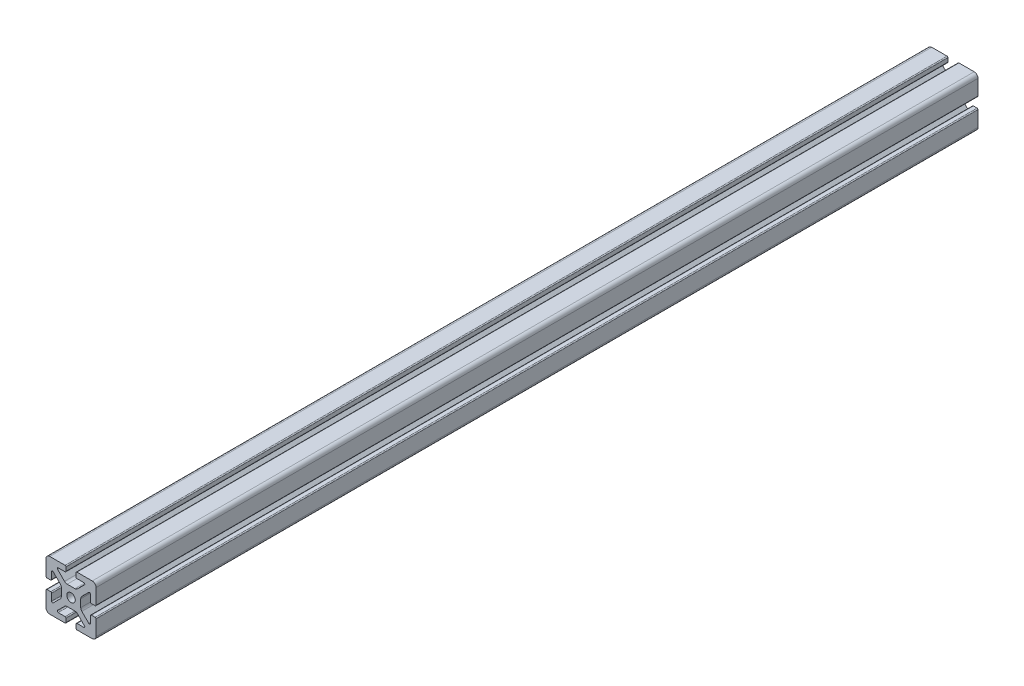
SolidWorks part; units mm, degrees
ref_plane "Front Plane" through (0, 0, 0) normal (0, 0, 1) x (1, 0, 0)
ref_plane "Top Plane" through (0, 0, 0) normal (0, 1, 0) x (1, 0, 0)
ref_plane "Right Plane" through (0, 0, 0) normal (1, 0, 0) x (0, 0, -1)
sketch "Sketch1" plane through (0, 0, 0) normal (0, 0, 1) x (1, 0, 0)
  line L2 (-20, 16.952) -> (-20, 4.7625)
  line L3 (-16.952, 20) -> (-4.7625, 20)
  line L4 (-4.0005, 19.238) -> (-4.0005, 16.2662)
  line L5 (-4.7625, 15.5042) -> (-10.2235, 15.5042)
  line L6 (-10.7623, 14.2034) -> (-5.194, 8.6351)
  line L7 (-14.2034, 10.7623) -> (-8.6351, 5.194)
  line L8 (-15.5042, 10.2235) -> (-15.5042, 4.7625)
  line L9 (-16.2662, 4.0005) -> (-19.238, 4.0005)
  line L11 (-3.0746, 7.7572) -> (3.0746, 7.7572)
  line L12 (-7.7572, 3.0746) -> (-7.7572, -3.0746)
  line L13 (16.2662, 4.0005) -> (19.238, 4.0005)
  line L14 (15.5042, 10.2235) -> (15.5042, 4.7625)
  line L15 (20, 16.952) -> (20, 4.7625)
  line L16 (16.952, 20) -> (4.7625, 20)
  line L17 (4.0005, 19.238) -> (4.0005, 16.2662)
  line L18 (4.7625, 15.5042) -> (10.2235, 15.5042)
  line L19 (7.7572, 3.0746) -> (7.7572, -3.0746)
  line L20 (10.7623, 14.2034) -> (5.194, 8.6351)
  line L21 (14.2034, 10.7623) -> (8.6351, 5.194)
  line L22 (-16.2662, -4.0005) -> (-19.238, -4.0005)
  line L23 (-15.5042, -10.2235) -> (-15.5042, -4.7625)
  line L24 (-14.2034, -10.7623) -> (-8.6351, -5.194)
  line L25 (-10.7623, -14.2034) -> (-5.194, -8.6351)
  line L26 (-4.7625, -15.5042) -> (-10.2235, -15.5042)
  line L27 (-4.0005, -19.238) -> (-4.0005, -16.2662)
  line L28 (-16.952, -20) -> (-4.7625, -20)
  line L29 (-20, -16.952) -> (-20, -4.7625)
  line L30 (20, -16.952) -> (20, -4.7625)
  line L31 (16.952, -20) -> (4.7625, -20)
  line L32 (4.0005, -19.238) -> (4.0005, -16.2662)
  line L33 (4.7625, -15.5042) -> (10.2235, -15.5042)
  line L34 (10.7623, -14.2034) -> (5.194, -8.6351)
  line L35 (14.2034, -10.7623) -> (8.6351, -5.194)
  line L36 (15.5042, -10.2235) -> (15.5042, -4.7625)
  line L37 (16.2662, -4.0005) -> (19.238, -4.0005)
  line L38 (-3.0746, -7.7572) -> (3.0746, -7.7572)
  circle A0 centre (0, 0) radius 3.4036
  arc A1 (-20, 16.952) -> (-16.952, 20) centre (-16.952, 16.952) cw
  arc A2 (-14.2034, 10.7623) -> (-15.5042, 10.2235) centre (-14.7422, 10.2235) ccw
  arc A3 (-10.2235, 15.5042) -> (-10.7623, 14.2034) centre (-10.2235, 14.7422) ccw
  arc A4 (-4.7625, 20) -> (-4.0005, 19.238) centre (-4.7625, 19.238) cw
  arc A5 (-20, 4.7625) -> (-19.238, 4.0005) centre (-19.238, 4.7625) ccw
  arc A6 (-15.5042, 4.7625) -> (-16.2662, 4.0005) centre (-16.2662, 4.7625) cw
  arc A7 (-4.0005, 16.2662) -> (-4.7625, 15.5042) centre (-4.7625, 16.2662) cw
  arc A8 (-3.0746, 7.7572) -> (-5.194, 8.6351) centre (-3.0746, 10.7544) cw
  arc A9 (-7.7572, 3.0746) -> (-8.6351, 5.194) centre (-10.7544, 3.0746) ccw
  arc A10 (15.5042, 4.7625) -> (16.2662, 4.0005) centre (16.2662, 4.7625) ccw
  arc A11 (20, 4.7625) -> (19.238, 4.0005) centre (19.238, 4.7625) cw
  arc A12 (20, 16.952) -> (16.952, 20) centre (16.952, 16.952) ccw
  arc A13 (4.7625, 20) -> (4.0005, 19.238) centre (4.7625, 19.238) ccw
  arc A14 (4.0005, 16.2662) -> (4.7625, 15.5042) centre (4.7625, 16.2662) ccw
  arc A15 (3.0746, 7.7572) -> (5.194, 8.6351) centre (3.0746, 10.7544) ccw
  arc A16 (7.7572, 3.0746) -> (8.6351, 5.194) centre (10.7544, 3.0746) cw
  arc A17 (14.2034, 10.7623) -> (15.5042, 10.2235) centre (14.7422, 10.2235) cw
  arc A18 (10.2235, 15.5042) -> (10.7623, 14.2034) centre (10.2235, 14.7422) cw
  arc A19 (-7.7572, -3.0746) -> (-8.6351, -5.194) centre (-10.7544, -3.0746) cw
  arc A20 (-3.0746, -7.7572) -> (-5.194, -8.6351) centre (-3.0746, -10.7544) ccw
  arc A21 (-4.0005, -16.2662) -> (-4.7625, -15.5042) centre (-4.7625, -16.2662) ccw
  arc A22 (-15.5042, -4.7625) -> (-16.2662, -4.0005) centre (-16.2662, -4.7625) ccw
  arc A23 (-20, -4.7625) -> (-19.238, -4.0005) centre (-19.238, -4.7625) cw
  arc A24 (-4.7625, -20) -> (-4.0005, -19.238) centre (-4.7625, -19.238) ccw
  arc A25 (-10.2235, -15.5042) -> (-10.7623, -14.2034) centre (-10.2235, -14.7422) cw
  arc A26 (-14.2034, -10.7623) -> (-15.5042, -10.2235) centre (-14.7422, -10.2235) cw
  arc A27 (-20, -16.952) -> (-16.952, -20) centre (-16.952, -16.952) ccw
  arc A28 (20, -16.952) -> (16.952, -20) centre (16.952, -16.952) cw
  arc A29 (14.2034, -10.7623) -> (15.5042, -10.2235) centre (14.7422, -10.2235) ccw
  arc A30 (10.2235, -15.5042) -> (10.7623, -14.2034) centre (10.2235, -14.7422) ccw
  arc A31 (4.7625, -20) -> (4.0005, -19.238) centre (4.7625, -19.238) cw
  arc A32 (20, -4.7625) -> (19.238, -4.0005) centre (19.238, -4.7625) ccw
  arc A33 (15.5042, -4.7625) -> (16.2662, -4.0005) centre (16.2662, -4.7625) cw
  arc A34 (4.0005, -16.2662) -> (4.7625, -15.5042) centre (4.7625, -16.2662) cw
  arc A35 (3.0746, -7.7572) -> (5.194, -8.6351) centre (3.0746, -10.7544) cw
  arc A36 (7.7572, -3.0746) -> (8.6351, -5.194) centre (10.7544, -3.0746) ccw
extrude "Boss-Extrude1" add sketch "Sketch1" along normal mid plane 705
